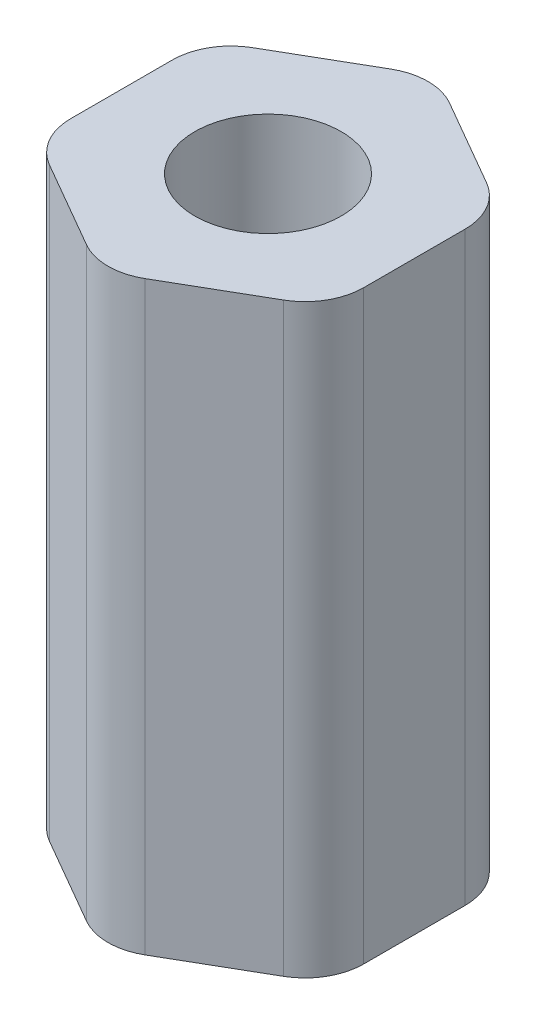
SolidWorks part; units mm, degrees
ref_plane "Front Plane" through (0, 0, 0) normal (0, 0, 1) x (1, 0, 0)
ref_plane "Top Plane" through (0, 0, 0) normal (0, 1, 0) x (1, 0, 0)
ref_plane "Right Plane" through (0, 0, 0) normal (1, 0, 0) x (0, 0, -1)
sketch "Sketch1" plane through (0, 0, 0) normal (0, 1, 0) x (1, 0, 0)
  line L1 (6.35, -3.6662) -> (6.35, 3.6662)
  line L2 (6.35, 3.6662) -> (0, 7.3323)
  line L3 (0, 7.3323) -> (-6.35, 3.6662)
  line L4 (-6.35, 3.6662) -> (-6.35, -3.6662)
  line L5 (-6.35, -3.6662) -> (0, -7.3323)
  line L6 (0, -7.3323) -> (6.35, -3.6662)
  circle A0 centre (0, 0) radius 6.35 construction
  circle A1 centre (0, 0) radius 3.175
  dimension "D2" = 6.35
  dimension "D1" = 12.7
extrude "Boss-Extrude1" add sketch "Sketch1" along normal blind 25.4
fillet "Fillet1" radius 2.54 6 edges at (-6.35, 12.7, 3.6662) (-6.35, 12.7, -3.6662) (0, 12.7, -7.3323) (6.35, 12.7, -3.6662) (6.35, 12.7, 3.6662) (0, 12.7, 7.3323)
